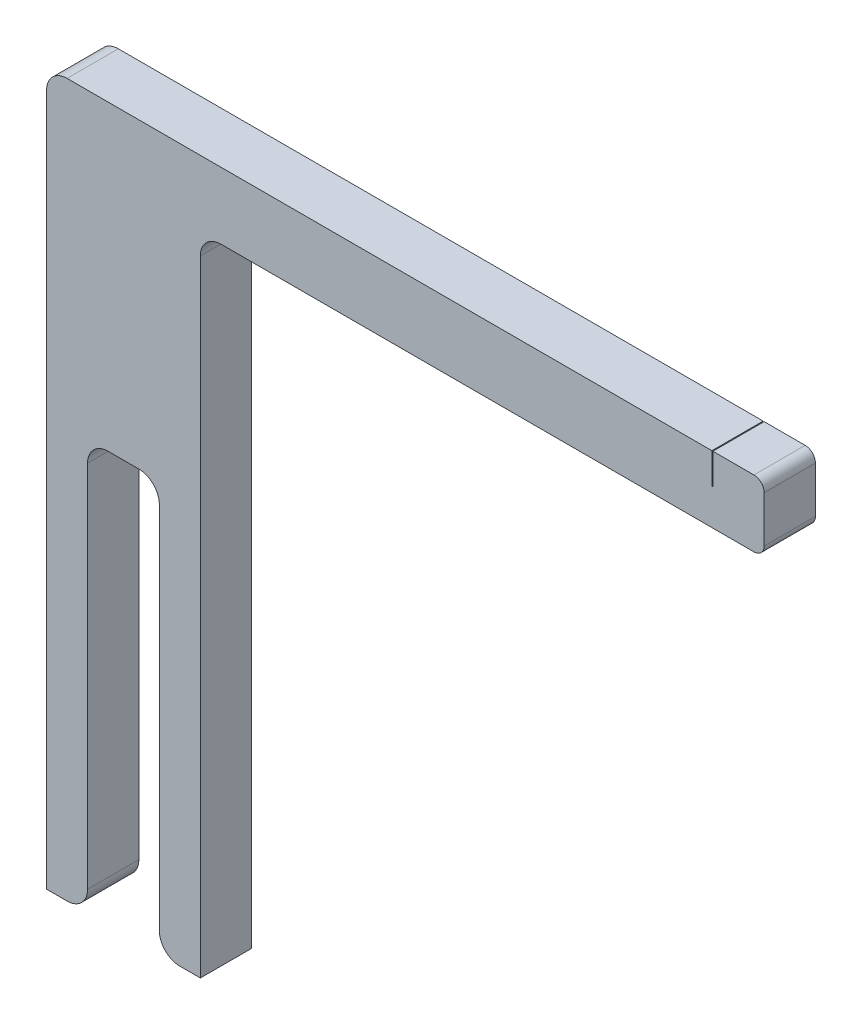
SolidWorks part; units mm, degrees
ref_plane "Front Plane" through (0, 0, 0) normal (0, 0, 1) x (1, 0, 0)
ref_plane "Top Plane" through (0, 0, 0) normal (0, 1, 0) x (1, 0, 0)
ref_plane "Right Plane" through (0, 0, 0) normal (1, 0, 0) x (0, 0, -1)
sketch "Sketch1" plane through (0, 0, 0) normal (0, 0, 1) x (1, 0, 0)
  line L0 (0, 0) -> (0, 67.5)
  line L1 (2, 69.5) -> (69, 69.5)
  line L2 (70, 68.5) -> (70, 64)
  line L3 (69, 63) -> (17, 63)
  line L4 (15, 61) -> (15, 0)
  line L5 (15, 0) -> (11, 0)
  line L6 (4, 0) -> (4, 40)
  line L7 (4, 40) -> (11, 40)
  line L8 (11, 40) -> (11, 0)
  line L9 (4, 0) -> (0, 0)
  arc A0 (17, 63) -> (15, 61) centre (17, 61) ccw
  arc A1 (2, 69.5) -> (0, 67.5) centre (2, 67.5) ccw
  arc A2 (70, 68.5) -> (69, 69.5) centre (69, 68.5) ccw
  arc A3 (69, 63) -> (70, 64) centre (69, 64) ccw
  point P11 (0, 69.5)
  point P14 (70, 69.5)
  point P17 (70, 63)
  dimension "D5" = 2
  dimension "D6" = 2
  dimension "D7" = 1
  dimension "D2" = 15
  dimension "D3" = 6.5
  dimension "D4" = 70
  dimension "D8" = 4
  dimension "D9" = 4
  dimension "D10" = 40
extrude "Boss-Extrude1" add sketch "Sketch1" along normal blind 5
sketch "Sketch3" plane through (0, 69.5, 0) normal (0, 1, 0) x (1, 0, 0)
  line L0 (0, -2.5) -> (64.95, -2.5) construction
  line L1 (0, -5) -> (0, 0) construction
  line L2 (69, 0) -> (2, 0) construction
  line L3 (64.9, -5) -> (65, -5)
  line L4 (64.9, -5) -> (64.9, 0)
  line L5 (64.9, 0) -> (65, 0)
  line L6 (65, -5) -> (65, 0)
  line L7 (64.9, -5) -> (65, 0) construction
  line L8 (64.9, 0) -> (65, -5) construction
  dimension "D1" = 64.95
  dimension "D2" = 0.1
extrude "Cut-Extrude1" cut sketch "Sketch3" against normal blind 3
fillet "Fillet1" radius 2 4 edges at (11, 0, 2.5) (4, 0, 2.5) (11, 40, 2.5) (4, 40, 2.5)
equation "\"A.L\"= 0.07m"
equation "\"A.h\"= 0.007m"
equation "\"A.d\"= 0.005m"
equation "\"A.delta\"= 45.0001"
equation "\"A.w\"= 0m"
equation "\"A.v\"= 0.013m"
equation "\"A.s\"= 0.014m"
equation "\"A.t\"= 0.007m"
equation "\"B.L\"= 0.065m"
equation "\"B.h\"= 0.008m"
equation "\"B.s\"= 0.016m"
equation "\"B.t\"= 0.008m"
equation "\"C.h\"= 0.0065m"
equation "\"C.d\"= 0.005m"
equation "\"C.L\"= 0.05m"
equation "\"C.wmax\"= 0.003m"
equation "\"D.L\"= 0.06m"
equation "\"D.h\"= 0.008m"
equation "\"D.s\"= 0.012m"
equation "\"D.t\"= 0.008m"
equation "\"a_h\"= 0.0001m"
equation "\"a_d\"= 0.005m"
equation "\"a_L\"= 0.008m"
equation "\"b_h\"= 0.0004m"
equation "\"b_d\"= 0.005m"
equation "\"b_L\"= 0.008m"
equation "\"c_h\"= 0.0001m"
equation "\"c_d\"= 0.005m"
equation "\"c_L\"= 0.01m"
equation "\"d_h\"= 0.0001m"
equation "\"d_d\"= 0.005m"
equation "\"d_L\"= 0.01m"
equation "\"S.h\"= 0.015m"
equation "\"S.L\"= 0.09175m"
equation "\"D1@Sketch1\"=\"C.h\"+\"C.wmax\"+60mm"
equation "\"D2@Sketch1\"=\"S.h\""
equation "\"D3@Sketch1\"=\"C.h\""
equation "\"D4@Sketch1\"=\"C.L\"+\"S.h\"+0.005"
equation "\"D1@Boss-Extrude1\"=0.005m"
equation "\"D1@Sketch3\"=\"C.L\"+\"S.h\"-\"c_h\"/2"
equation "\"D2@Sketch3\"=\"c_h\""
